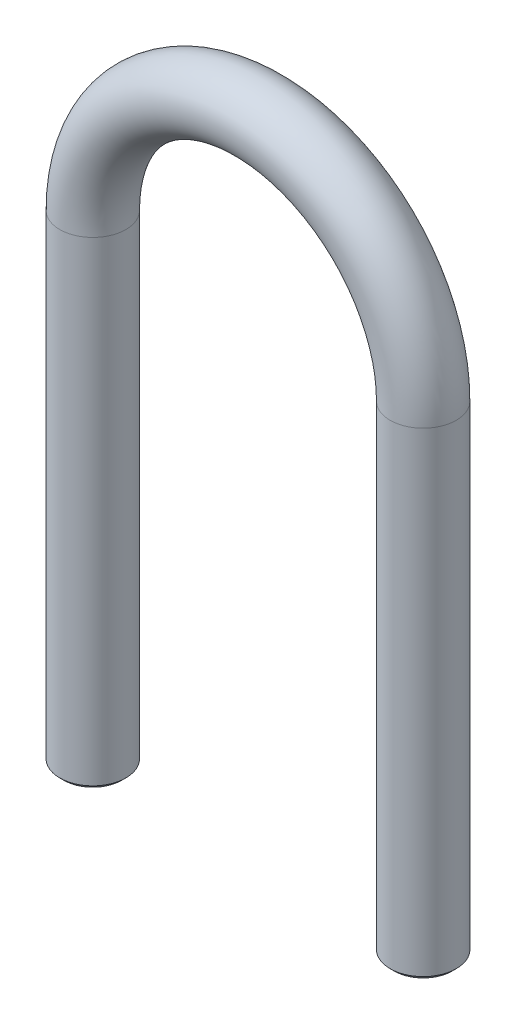
SolidWorks part; units mm, degrees
ref_plane "Front" through (0, 0, 0) normal (0, 0, 1) x (1, 0, 0)
ref_plane "Top" through (0, 0, 0) normal (0, 1, 0) x (1, 0, 0)
ref_plane "Right" through (0, 0, 0) normal (1, 0, 0) x (0, 0, -1)
sketch "Sketch1" plane through (0, 0, 0) normal (0, 0, 1) x (1, 0, 0)
  line L0 (-20, 0) -> (-20, -58)
  line L1 (0, 26.657) -> (0, -24.7278) construction
  line L2 (20, 0) -> (20, -58)
  arc A0 (-20, 0) -> (20, 0) centre (0, 0) cw
  dimension "D1" = 20
  dimension "D2" = 58
ref_plane "Plane1" through (0, -58, 0) normal (0, 1, 0) x (1, 0, 0)
sketch "Sketch2" plane through (0, -58, 0) normal (0, 1, 0) x (1, 0, 0)
  line L0 (-20, 0) -> (20, 0) construction
  circle A0 centre (-20, 0) radius 4
  dimension "D1" = 8
  dimension "D2" = 20
sweep "Sweep1" add profiles "Sketch2" path "Sketch1"
chamfer "Chamfer1" distance 0.5 angle 45 2 edges at (20, -58, 4) (-20, -58, 4)
